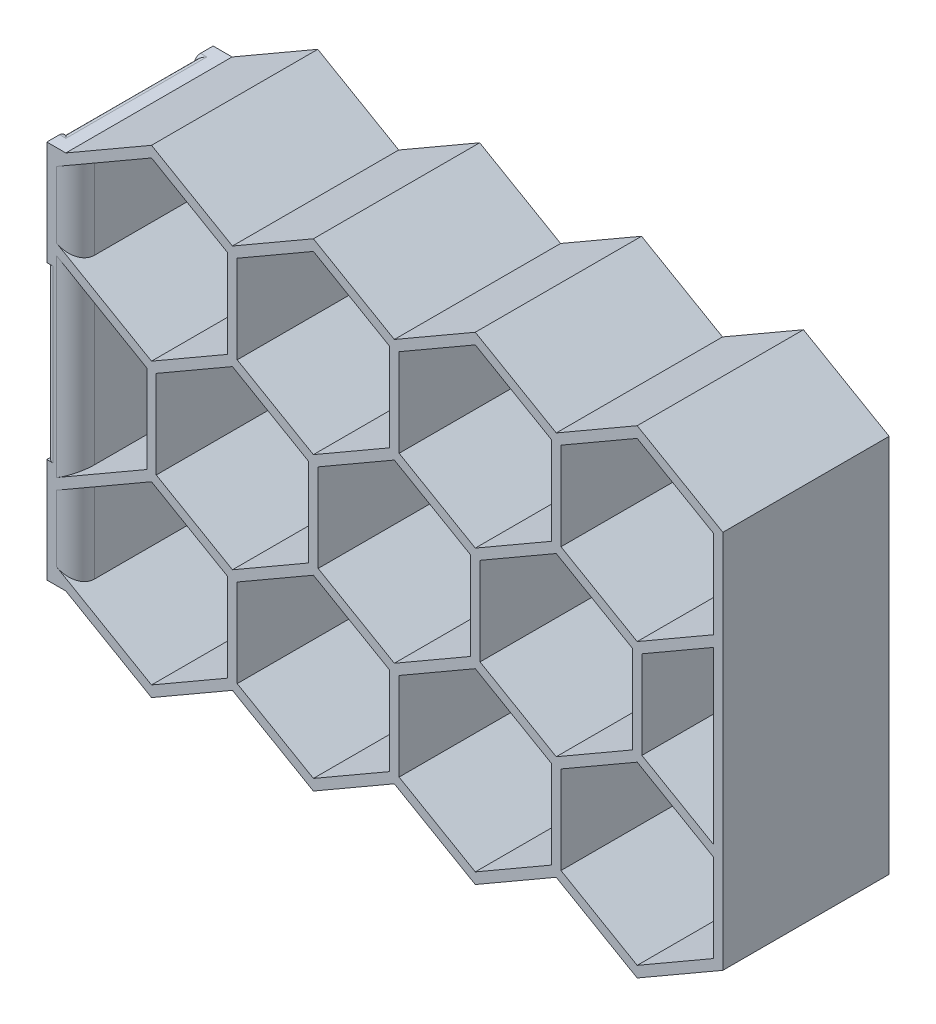
SolidWorks part; units mm, degrees
ref_plane "Front Plane" through (0, 0, 0) normal (0, 0, 1) x (1, 0, 0)
ref_plane "Top Plane" through (0, 0, 0) normal (0, 1, 0) x (1, 0, 0)
ref_plane "Right Plane" through (0, 0, 0) normal (1, 0, 0) x (0, 0, -1)
sketch "Sketch1" plane through (0, 0, 0) normal (0, 1, 0) x (1, 0, 0)
  line L1 (0, 0) -> (20.3, 0)
  line L2 (0, 0) -> (0, 20.3)
  line L3 (0, 20.3) -> (20.3, 20.3)
  line L4 (20.3, 0) -> (20.3, 20.3)
  line L5 (-3, -3) -> (23.3, -3)
  line L6 (-3, -3) -> (-3, 23.3)
  line L7 (-3, 23.3) -> (23.3, 23.3)
  line L8 (23.3, -3) -> (23.3, 23.3)
  line L9 (20.3, 20.3) -> (23.3, 20.3) construction
  line L10 (20.3, 20.3) -> (20.3, 23.3) construction
  line L11 (20.3, 23.3) -> (23.3, 23.3) construction
  line L12 (23.3, 20.3) -> (23.3, 23.3) construction
  line L13 (0, 0) -> (-3, 0) construction
  line L14 (0, 0) -> (0, -3) construction
  line L15 (0, -3) -> (-3, -3) construction
  line L16 (-3, 0) -> (-3, -3) construction
  dimension "D1" = 20.3
  dimension "D2" = 3
extrude "Tube Extrude" add sketch "Sketch1" along normal blind 60
ref_plane "tube outer plane" through (0, 0, 3) normal (0, 0, 1) x (1, 0, 0)
sketch "Sketch2" plane through (0, 0, 3) normal (0, 0, 1) x (1, 0, 0)
  line L0 (23.3, 60) -> (23.3, 0) construction
  line L1 (49.6558, 16.0825) -> (37.6029, 23.0413)
  line L2 (36.1029, 23.0413) -> (24.8, 16.5155)
  line L3 (23.3, 15.6495) -> (23.3, 0)
  line L4 (23.3, 0) -> (36.8529, -7.8248)
  line L5 (36.8529, -7.8248) -> (49.6558, -0.433)
  line L6 (50.4058, 0.866) -> (50.4058, 14.7835) construction
  line L7 (75.2615, 16.0825) -> (62.4586, 23.4743) construction
  line L8 (24.8, 0.866) -> (36.8529, -6.0927)
  line L9 (36.8529, -6.0927) -> (48.9058, 0.866)
  line L10 (48.9058, 0.866) -> (48.9058, 14.7835)
  line L11 (48.9058, 14.7835) -> (36.8529, 21.7422)
  line L12 (36.8529, 21.7422) -> (24.8, 14.7835)
  line L13 (24.8, 14.7835) -> (24.8, 0.866)
  line L14 (62.4586, 23.4743) -> (49.6558, 16.0825) construction
  line L15 (48.9058, 14.7835) -> (48.9058, 0.866) construction
  line L16 (49.6558, -0.433) -> (62.4586, -7.8248)
  line L17 (62.4586, -7.8248) -> (75.2615, -0.433)
  line L18 (76.0115, 0.866) -> (76.0115, 14.7835) construction
  line L19 (50.4058, 0.866) -> (62.4586, -6.0927)
  line L20 (62.4586, -6.0927) -> (74.5115, 0.866)
  line L21 (74.5115, 0.866) -> (74.5115, 14.7835)
  line L22 (74.5115, 14.7835) -> (62.4586, 21.7422)
  line L23 (62.4586, 21.7422) -> (50.4058, 14.7835)
  line L24 (50.4058, 14.7835) -> (50.4058, 0.866)
  line L25 (100.8673, 16.0825) -> (88.0644, 23.4743) construction
  line L26 (88.0644, 23.4743) -> (75.2615, 16.0825) construction
  line L27 (74.5115, 14.7835) -> (74.5115, 0.866) construction
  line L28 (75.2615, -0.433) -> (88.0644, -7.8248)
  line L29 (88.0644, -7.8248) -> (100.8673, -0.433)
  line L30 (101.6173, 0.866) -> (101.6173, 14.7835) construction
  line L31 (76.0115, 0.866) -> (88.0644, -6.0927)
  line L32 (88.0644, -6.0927) -> (100.1173, 0.866)
  line L33 (100.1173, 0.866) -> (100.1173, 14.7835)
  line L34 (100.1173, 14.7835) -> (88.0644, 21.7422)
  line L35 (88.0644, 21.7422) -> (76.0115, 14.7835)
  line L36 (76.0115, 14.7835) -> (76.0115, 0.866)
  line L37 (125.723, 16.5155) -> (114.4202, 23.0413)
  line L38 (112.9202, 23.0413) -> (100.8673, 16.0825) construction
  line L39 (100.1173, 14.7835) -> (100.1173, 0.866) construction
  line L40 (100.8673, -0.433) -> (113.6702, -7.8248)
  line L41 (113.6702, -7.8248) -> (127.223, 0)
  line L42 (127.223, 0) -> (127.223, 15.6495)
  line L43 (101.6173, 0.866) -> (113.6702, -6.0927)
  line L44 (113.6702, -6.0927) -> (125.723, 0.866)
  line L45 (125.723, 0.866) -> (125.723, 14.7835)
  line L46 (125.723, 14.7835) -> (113.6702, 21.7422)
  line L47 (113.6702, 21.7422) -> (101.6173, 14.7835)
  line L48 (101.6173, 14.7835) -> (101.6173, 0.866)
  line L85 (49.6558, 60.433) -> (36.8529, 67.8248)
  line L86 (36.8529, 67.8248) -> (23.3, 60)
  line L87 (23.3, 60) -> (23.3, 44.3505)
  line L88 (24.8, 43.4845) -> (36.1029, 36.9587)
  line L89 (37.6029, 36.9587) -> (49.6558, 43.9175) construction
  line L90 (75.2615, 60.433) -> (62.4586, 67.8248)
  line L91 (24.8, 45.2165) -> (36.8529, 38.2578)
  line L92 (36.8529, 38.2578) -> (48.9058, 45.2165)
  line L93 (48.9058, 45.2165) -> (48.9058, 59.134)
  line L94 (48.9058, 59.134) -> (36.8529, 66.0927)
  line L95 (36.8529, 66.0927) -> (24.8, 59.134)
  line L96 (24.8, 59.134) -> (24.8, 45.2165)
  line L97 (62.4586, 67.8248) -> (49.6558, 60.433)
  line L98 (49.6558, 43.9175) -> (62.4586, 36.5257) construction
  line L99 (62.4586, 36.5257) -> (75.2615, 43.9175) construction
  line L100 (50.4058, 45.2165) -> (62.4586, 38.2578)
  line L101 (62.4586, 38.2578) -> (74.5115, 45.2165)
  line L102 (74.5115, 45.2165) -> (74.5115, 59.134)
  line L103 (74.5115, 59.134) -> (62.4586, 66.0927)
  line L104 (62.4586, 66.0927) -> (50.4058, 59.134)
  line L105 (50.4058, 59.134) -> (50.4058, 45.2165)
  line L106 (100.8673, 60.433) -> (88.0644, 67.8248)
  line L107 (88.0644, 67.8248) -> (75.2615, 60.433)
  line L108 (75.2615, 43.9175) -> (88.0644, 36.5257) construction
  line L109 (88.0644, 36.5257) -> (100.8673, 43.9175) construction
  line L110 (76.0115, 45.2165) -> (88.0644, 38.2578)
  line L111 (88.0644, 38.2578) -> (100.1173, 45.2165)
  line L112 (100.1173, 45.2165) -> (100.1173, 59.134)
  line L113 (100.1173, 59.134) -> (88.0644, 66.0927)
  line L114 (88.0644, 66.0927) -> (76.0115, 59.134)
  line L115 (76.0115, 59.134) -> (76.0115, 45.2165)
  line L116 (127.223, 60) -> (113.6702, 67.8248)
  line L117 (113.6702, 67.8248) -> (100.8673, 60.433)
  line L118 (100.8673, 43.9175) -> (113.6702, 36.5257) construction
  line L119 (114.4202, 36.9587) -> (125.723, 43.4845)
  line L120 (127.223, 44.3505) -> (127.223, 60)
  line L121 (101.6173, 45.2165) -> (113.6702, 38.2578)
  line L122 (113.6702, 38.2578) -> (125.723, 45.2165)
  line L123 (125.723, 45.2165) -> (125.723, 59.134)
  line L124 (125.723, 59.134) -> (113.6702, 66.0927)
  line L125 (113.6702, 66.0927) -> (101.6173, 59.134)
  line L126 (101.6173, 59.134) -> (101.6173, 45.2165)
  line L127 (50.4058, 45.2165) -> (50.4058, 59.134) construction
  line L128 (48.9058, 59.134) -> (48.9058, 45.2165) construction
  line L129 (76.0115, 45.2165) -> (76.0115, 59.134) construction
  line L130 (74.5115, 59.134) -> (74.5115, 45.2165) construction
  line L131 (101.6173, 45.2165) -> (101.6173, 59.134) construction
  line L132 (100.1173, 59.134) -> (100.1173, 45.2165) construction
  line L133 (114.4202, 23.0413) -> (114.4202, 22.1752) construction
  line L134 (62.4586, 21.7422) -> (75.2615, 14.3505) construction
  line L135 (36.8529, 21.7422) -> (49.6558, 14.3505) construction
  line L136 (49.6558, 14.3505) -> (62.4586, 21.7422) construction
  line L137 (63.2086, 23.0413) -> (63.2086, 36.9587) construction
  line L138 (62.4586, 38.2578) -> (49.6558, 45.6495) construction
  line L139 (49.6558, 45.6495) -> (36.8529, 38.2578) construction
  line L140 (36.1029, 36.9587) -> (36.1029, 23.0413)
  line L141 (49.6558, 16.0825) -> (61.7086, 23.0413)
  line L142 (61.7086, 23.0413) -> (61.7086, 36.9587)
  line L143 (61.7086, 36.9587) -> (49.6558, 43.9175)
  line L144 (49.6558, 43.9175) -> (37.6029, 36.9587)
  line L145 (37.6029, 36.9587) -> (37.6029, 23.0413)
  line L146 (37.6029, 23.0413) -> (49.6558, 16.0825)
  line L147 (75.2615, 14.3505) -> (88.0644, 21.7422) construction
  line L148 (88.8144, 23.0413) -> (88.8144, 36.9587) construction
  line L149 (88.0644, 38.2578) -> (75.2615, 45.6495) construction
  line L150 (75.2615, 45.6495) -> (62.4586, 38.2578) construction
  line L151 (61.7086, 36.9587) -> (61.7086, 23.0413) construction
  line L152 (75.2615, 16.0825) -> (87.3144, 23.0413)
  line L153 (87.3144, 23.0413) -> (87.3144, 36.9587)
  line L154 (87.3144, 36.9587) -> (75.2615, 43.9175)
  line L155 (75.2615, 43.9175) -> (63.2086, 36.9587)
  line L156 (63.2086, 36.9587) -> (63.2086, 23.0413)
  line L157 (63.2086, 23.0413) -> (75.2615, 16.0825)
  line L158 (88.0644, 21.7422) -> (100.8673, 14.3505) construction
  line L159 (100.8673, 14.3505) -> (114.4202, 22.1752) construction
  line L160 (114.4202, 23.0413) -> (114.4202, 36.9587)
  line L161 (113.6702, 38.2578) -> (100.8673, 45.6495) construction
  line L162 (100.8673, 45.6495) -> (88.0644, 38.2578) construction
  line L163 (87.3144, 36.9587) -> (87.3144, 23.0413) construction
  line L164 (100.8673, 16.0825) -> (112.9202, 23.0413)
  line L165 (112.9202, 23.0413) -> (112.9202, 36.9587)
  line L166 (112.9202, 36.9587) -> (100.8673, 43.9175)
  line L167 (100.8673, 43.9175) -> (88.8144, 36.9587)
  line L168 (88.8144, 36.9587) -> (88.8144, 23.0413)
  line L169 (88.8144, 23.0413) -> (100.8673, 16.0825)
  line L170 (114.4202, 36.9587) -> (113.6702, 36.5257)
  line L171 (127.223, 44.3505) -> (127.223, 15.6495)
  line L172 (125.723, 16.5155) -> (125.723, 43.4845)
  line L173 (23.3, 15.6495) -> (23.3, 44.3505)
  line L174 (24.8, 16.5155) -> (24.8, 43.4845)
  line L180 (-3, 60) -> (23.3, 60) construction
  circle A0 centre (36.8529, 7.8248) radius 13.5529 construction
  circle A1 centre (36.8529, 7.8248) radius 12.0529 construction
  circle A2 centre (62.4586, 7.8248) radius 13.5529 construction
  circle A3 centre (62.4586, 7.8248) radius 12.0529 construction
  circle A4 centre (88.0644, 7.8248) radius 13.5529 construction
  circle A5 centre (88.0644, 7.8248) radius 12.0529 construction
  circle A6 centre (113.6702, 7.8248) radius 13.5529 construction
  circle A7 centre (113.6702, 7.8248) radius 12.0529 construction
  circle A8 centre (49.6558, 30) radius 13.5529 construction
  circle A9 centre (49.6558, 30) radius 12.0529 construction
  circle A10 centre (75.2615, 30) radius 13.5529 construction
  circle A11 centre (75.2615, 30) radius 12.0529 construction
  circle A12 centre (100.8673, 30) radius 13.5529 construction
  circle A13 centre (100.8673, 30) radius 12.0529 construction
  circle A14 centre (36.8529, 52.1752) radius 13.5529 construction
  circle A15 centre (36.8529, 52.1752) radius 12.0529 construction
  circle A16 centre (62.4586, 52.1752) radius 13.5529 construction
  circle A17 centre (62.4586, 52.1752) radius 12.0529 construction
  circle A18 centre (88.0644, 52.1752) radius 13.5529 construction
  circle A19 centre (88.0644, 52.1752) radius 12.0529 construction
  circle A20 centre (113.6702, 52.1752) radius 13.5529 construction
  circle A21 centre (113.6702, 52.1752) radius 12.0529 construction
  dimension "D1" = 0
  dimension "D2" = 1.5
  dimension "D3" = 4
  dimension "D5" = 2
  dimension "D4" = 3
extrude "Hex Extrude" add sketch "Sketch2" against normal up to surface (26.3 mm away) contours L12 L13 L8 L9 L10 L11 | L23 L24 L19 L20 L21 L22 | L144 L145 L1 L141 L142 L143 | L174 L2 L140 L88 | L95 L96 L91 L92 L93 L94 | L104 L105 L100 L101 L102 L103 | L156 L157 L152 L153 L154 L155 | L35 L36 L31 L32 L33 L34 | L168 L169 L164 L165 L166 L167 | L114 L115 L110 L111 L112 L113 | L125 L126 L121 L122 L123 L124 | L47 L48 L43 L44 L45 L46 | L37 L172 L119 L160 | L16 L17 L28 L29 L40 L41 L42 L171 L120 L116 L117 L106 L107 L90 L97 L85 L86 L87 L173 L3 L4 L5
sketch "Sketch3" plane through (0, 0, 3) normal (0, 0, 1) x (1, 0, 0)
  line L0 (-3, 60) -> (-3, 0) construction
  line L1 (20.3, 43.4845) -> (-3, 43.4845)
  line L2 (20.3, 43.4845) -> (20.3, 16.5155)
  line L3 (20.3, 16.5155) -> (-3, 16.5155)
  line L4 (-3, 43.4845) -> (-3, 16.5155)
  line L5 (20.3, 43.4845) -> (24.8, 43.4845) construction
  line L6 (20.3, 16.5155) -> (24.8, 16.5155) construction
extrude "Tube Center Cut" cut sketch "Sketch3" against normal through all both and the other way through all
ref_plane "Plane1" through (-3, 0, 0) normal (-1, 0, 0) x (0, 0, 1)
sketch "Sketch4" plane through (-3, 0, 0) normal (-1, 0, 0) x (0, 0, 1)
  line L0 (-10.15, 60) -> (-10.35, 60)
  line L1 (-23.3, 60) -> (3, 60) construction
  line L2 (-10.35, 60) -> (-10.35, 0)
  line L3 (-23.3, 0) -> (3, 0) construction
  line L4 (-10.35, 0) -> (-10.15, 0)
  line L5 (-10.15, 0) -> (-9.95, 0)
  line L6 (-9.95, 0) -> (-9.95, 60)
  line L7 (-9.95, 60) -> (-10.15, 60)
  dimension "D1" = 0.2
extrude "Cut-Extrude1" cut sketch "Sketch4" against normal up to next
sketch "Sketch5" plane through (0, 0, 3) normal (0, 0, 1) x (1, 0, 0)
  line L0 (-3, 7.1225) -> (-3, -7.1225) construction
  line L1 (-3, 57) -> (-2, 57)
  line L2 (-3, 57) -> (-3, 46.4845)
  line L3 (-3, 46.4845) -> (-2, 46.4845)
  line L4 (-2, 57) -> (-2, 46.4845)
  line L5 (20.3, 30) -> (-9.7, 30) construction
  line L6 (20.3, 43.4845) -> (20.3, 16.5155) construction
  line L7 (-2, 57) -> (-2, 60) construction
  line L8 (-3, 60) -> (23.3, 60) construction
  line L9 (-2, 46.4845) -> (-2, 43.4845) construction
  line L10 (-3, 43.4845) -> (20.3, 43.4845) construction
  line L11 (-2, 3) -> (-2, 13.5155)
  line L12 (-3, 13.5155) -> (-2, 13.5155)
  line L13 (-3, 3) -> (-3, 13.5155)
  line L14 (-3, 3) -> (-2, 3)
  dimension "D1" = 30
  dimension "D2" = 3
  dimension "D3" = 1
extrude "Cut-Extrude2" cut sketch "Sketch5" against normal through all
fillet "Fillet1" radius 3 10 edges at (24.8, 7.8248, -23.3) (24.8, 7.8248, 3) (24.8, 52.1752, -23.3) (24.8, 52.1752, 3) (-2, 51.7422, -23.3) (-2, 51.7422, 3) (-2, 8.2578, 3) (-2, 8.2578, -23.3) (24.8, 30, -23.3) (24.8, 30, 3)
fillet "Fillet2" radius 1 28 edges at (20.3, 30, -23.3) (20.3, 30, 3) (10.15, 16.5155, -20.3) (0, 16.5155, -15.325) (0, 16.5155, -4.975) (10.15, 16.5155, 0) (10.15, 0, -20.3) (0, 0, -15.325) (0, 0, -4.975) (20.3, 0, -10.15) (10.15, 0, 0) (10.15, 43.4845, 0) (0, 43.4845, -4.975) (0, 43.4845, -15.325) (10.15, 43.4845, -20.3) (0, 60, -4.975) (0, 60, -15.325) (10.15, 60, -20.3) (10.15, 60, 0) (20.3, 60, -10.15) (-3, 44.9845, -23.3) (-3, 58.5, -23.3) (-3, 44.9845, 3) (-3, 58.5, 3) (-3, 1.5, 3) (-3, 15.0155, 3) (-3, 1.5, -23.3) (-3, 15.0155, -23.3)
sketch "Sketch6" plane through (0, 0, 3) normal (0, 0, 1) x (1, 0, 0)
  line L0 (-3, 1.65) -> (-3, -1.65) construction
  line L1 (-3, 60) -> (20.3, 60)
  line L2 (-3, 60) -> (-3, 0)
  line L3 (-3, 0) -> (20.3, 0)
  line L4 (20.3, 60) -> (20.3, 0)
  line L5 (-2, 60) -> (-3, 60) construction
  line L7 (-2, 0) -> (23.3, 0) construction
  line L8 (20.3, 16.5155) -> (20.3, 43.4845) construction
  point P9 (0, 0)
extrude "Cut-Extrude3" cut sketch "Sketch6" against normal through all
